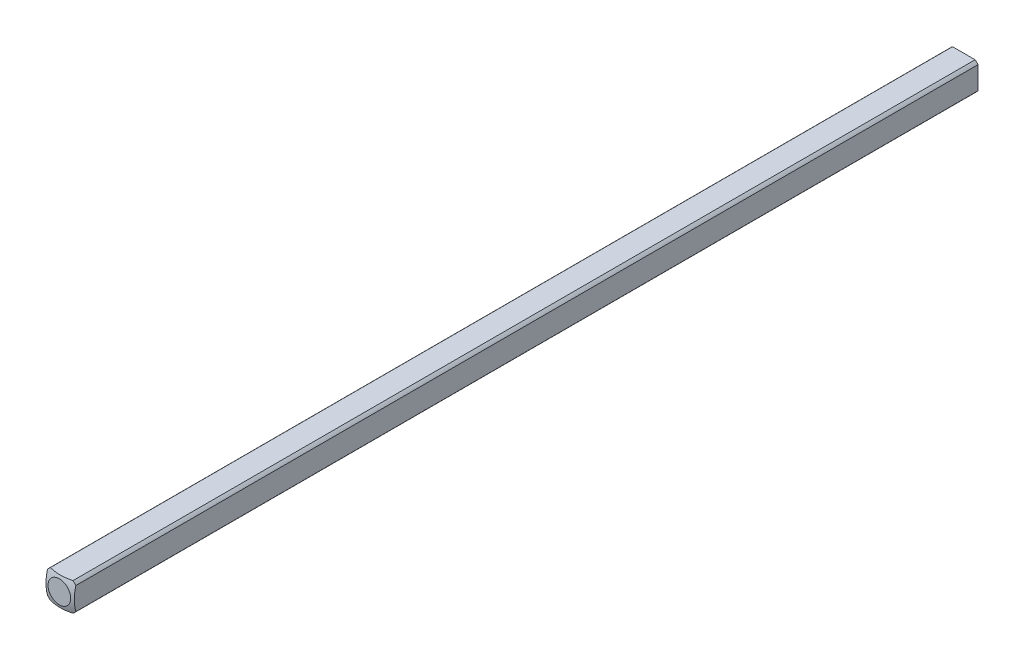
SolidWorks part; units mm, degrees
material "Custom Plastic"
ref_plane "Front Plane" through (0, 0, 0) normal (0, 0, 1) x (1, 0, 0)
ref_plane "Top Plane" through (0, 0, 0) normal (0, 1, 0) x (1, 0, 0)
ref_plane "Right Plane" through (0, 0, 0) normal (1, 0, 0) x (0, 0, -1)
sketch "Sketch1" plane through (0, 0, 0) normal (0, 0, 1) x (1, 0, 0)
  line L0 (-1.5875, -1.5875) -> (1.5875, 1.5875) construction
  line L1 (-1.5875, -1.5875) -> (1.5875, -1.5875)
  line L2 (-1.5875, -1.5875) -> (-1.5875, 1.5875)
  line L3 (-1.5875, 1.5875) -> (1.5875, 1.5875)
  line L4 (1.5875, -1.5875) -> (1.5875, 1.5875)
  dimension "D1" = 3.175
extrude "Boss-Extrude1" add sketch "Sketch1" along normal blind 152.4
sketch "Sketch2" plane through (0, 0, 0) normal (0, 0, -1) x (-1, 0, 0)
  circle A0 centre (0, 0) radius 2.032
  dimension "D1" = 4.064
extrude "Cut-Extrude1" cut sketch "Sketch2" against normal through all flip side to cut
ref_axis "Axis1" through (0, 0, 152.4) along (0, 0, -1)
sketch "Sketch3" plane through (0, 0, 0) normal (0, 1, 0) x (1, 0, 0)
  line L1 (-5.0537, -4.4027) -> (-5.0537, 5.7405)
  line L2 (-5.0537, 5.7405) -> (0, 5.7405)
  line L5 (0, -152.4) -> (0, 0) construction
  line L8 (0, 0.1609) -> (0, 5.7405)
  arc A0 (-5.0537, -4.4027) -> (0, 0.1609) centre (0, -4.9191) cw
  dimension "D1" = 5.08
revolve "Cut-Revolve1" cut sketch "Sketch3" angle 360 about axis through (0, 0, 152.4) along (0, 0, -1)
mirror "Mirror1" about plane through (0, 0, 152.4) normal (0, 0, -1) of bodies 103
sketch "Sketch4" plane through (1.5875, 0, 0) normal (1, 0, 0) x (0, 0, -1)
  line L1 (-0.2632, -1.5875) -> (-203.4632, -1.5875)
  line L2 (-0.2632, 1.5875) -> (-203.4632, 1.5875)
  line L3 (-203.4632, -1.5875) -> (-203.4632, 1.5875)
  line L4 (-0.2632, -1.5875) -> (0.8357, -1.5875)
  line L5 (0.8357, -1.5875) -> (0.8357, 1.5875)
  line L6 (0.8357, 1.5875) -> (-0.2632, 1.5875)
  dimension "D1" = 203.2
extrude "Cut-Extrude2" cut sketch "Sketch4" against normal through all
